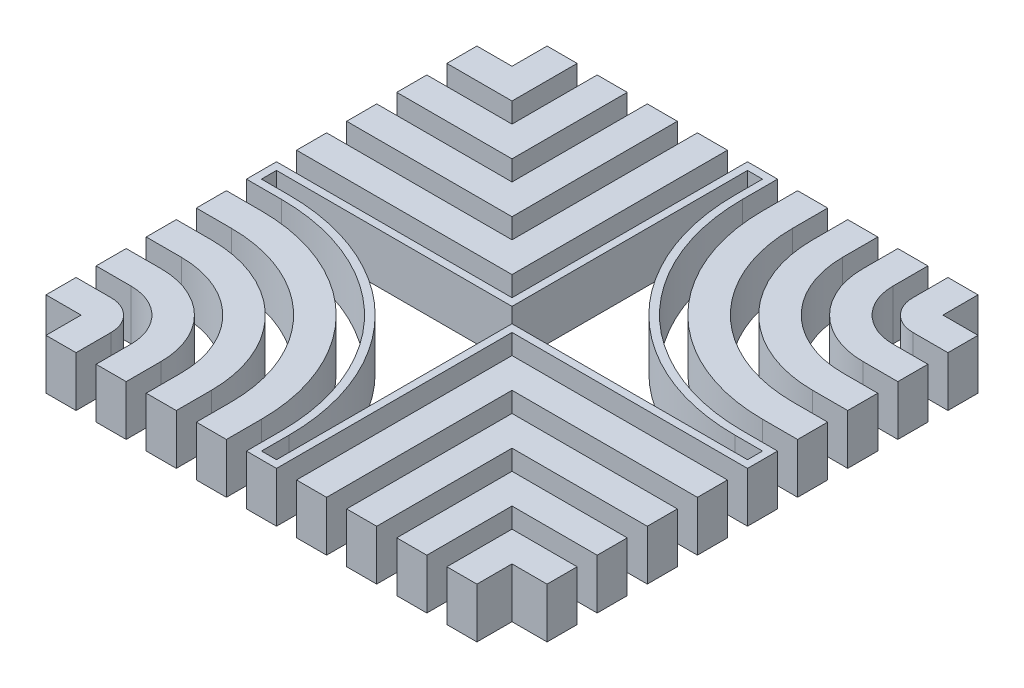
SolidWorks part; units mm, degrees
ref_plane "Front Plane" through (0, 0, 0) normal (0, 0, 1) x (1, 0, 0)
ref_plane "Top Plane" through (0, 0, 0) normal (0, 1, 0) x (1, 0, 0)
ref_plane "Right Plane" through (0, 0, 0) normal (1, 0, 0) x (0, 0, -1)
sketch "Sketch1" plane through (0, 0, 0) normal (0, 1, 0) x (1, 0, 0)
  line L0 (0, 50) -> (0, -50) construction
  line L1 (-50, 0) -> (50, 0) construction
  line L2 (-50, -10) -> (-10, -10) construction
  line L3 (-10, 50) -> (-10, 10) construction
  line L4 (-50, 10) -> (-10, 10) construction
  line L5 (10, 50) -> (10, 10) construction
  line L6 (10, 10) -> (50, 10) construction
  line L7 (-50, 10) -> (50, 10) construction
  line L8 (-10, -10) -> (-10, -50) construction
  line L9 (-10, 50) -> (-10, -50) construction
  line L10 (10, -10) -> (10, -50) construction
  line L11 (10, 50) -> (10, -50) construction
  line L12 (10, -10) -> (50, -10) construction
  line L13 (-50, -10) -> (50, -10) construction
  line L14 (-20, 50) -> (-20, 20) construction
  line L15 (-50, 20) -> (-20, 20) construction
  line L16 (20, 50) -> (20, 20) construction
  line L17 (20, 20) -> (50, 20) construction
  line L18 (20, -20) -> (20, -50) construction
  line L19 (20, -20) -> (50, -20) construction
  line L20 (-50, -20) -> (-20, -20) construction
  line L21 (-20, -20) -> (-20, -50) construction
  line L22 (-50, -30) -> (-30, -30) construction
  line L23 (-30, -30) -> (-30, -50) construction
  line L24 (30, -30) -> (30, -50) construction
  line L25 (30, -30) -> (50, -30) construction
  line L26 (30, 50) -> (30, 30) construction
  line L27 (30, 30) -> (50, 30) construction
  line L28 (-50, 30) -> (-30, 30) construction
  line L29 (-30, 50) -> (-30, 30) construction
  line L30 (-50, -40) -> (-40, -40) construction
  line L31 (-40, -40) -> (-40, -50) construction
  line L32 (40, -40) -> (40, -50) construction
  line L33 (40, -40) -> (50, -40) construction
  line L34 (-50, 40) -> (-40, 40) construction
  line L35 (-40, 50) -> (-40, 40) construction
  line L36 (40, 50) -> (40, 40) construction
  line L37 (40, 40) -> (50, 40) construction
  line L38 (-50, 37) -> (-37, 37)
  line L39 (-37, 50) -> (-37, 37)
  line L40 (-50, 27) -> (-27, 27)
  line L41 (-27, 50) -> (-27, 27)
  line L42 (-50, 17) -> (-17, 17)
  line L43 (-17, 50) -> (-17, 17)
  line L44 (-50, 7) -> (-7, 7)
  line L45 (-7, 50) -> (-7, 7)
  line L46 (-50, -3) -> (-43, -3)
  line L47 (-50, 43) -> (-43, 43)
  line L48 (-43, 50) -> (-43, 43)
  line L49 (-50, 33) -> (-33, 33)
  line L50 (-33, 50) -> (-33, 33)
  line L51 (-50, 23) -> (-23, 23)
  line L52 (-23, 50) -> (-23, 23)
  line L53 (-50, 13) -> (-13, 13)
  line L54 (-13, 50) -> (-13, 13)
  line L55 (-50, 3) -> (-3, 3)
  line L56 (-50, -13) -> (-43, -13)
  line L57 (-13, -43) -> (-13, -50)
  line L58 (-50, -23) -> (-43, -23)
  line L59 (-23, -43) -> (-23, -50)
  line L60 (-50, -33) -> (-43, -33)
  line L61 (-33, -43) -> (-33, -50)
  line L62 (-50, -43) -> (-43, -43)
  line L63 (-43, -43) -> (-43, -50)
  line L64 (7, -7) -> (50, -7)
  line L65 (7, -7) -> (7, -50)
  line L66 (17, -17) -> (50, -17)
  line L67 (17, -17) -> (17, -50)
  line L68 (27, -27) -> (50, -27)
  line L69 (27, -27) -> (27, -50)
  line L70 (37, -37) -> (50, -37)
  line L71 (37, -37) -> (37, -50)
  line L72 (7, 50) -> (7, 43)
  line L73 (43, 7) -> (50, 7)
  line L74 (-50, -7) -> (-43, -7)
  line L75 (-7, -43) -> (-7, -50)
  line L76 (-50, -17) -> (-43, -17)
  line L77 (-17, -43) -> (-17, -50)
  line L78 (-50, -27) -> (-43, -27)
  line L79 (-27, -43) -> (-27, -50)
  line L80 (-50, -37) -> (-43, -37)
  line L81 (-37, -43) -> (-37, -50)
  line L82 (13, -13) -> (50, -13)
  line L83 (13, -13) -> (13, -50)
  line L84 (23, -23) -> (50, -23)
  line L85 (23, -23) -> (23, -50)
  line L86 (33, -33) -> (50, -33)
  line L87 (33, -33) -> (33, -50)
  line L88 (43, -43) -> (50, -43)
  line L89 (43, -43) -> (43, -50)
  line L90 (13, 50) -> (13, 43)
  line L91 (43, 13) -> (50, 13)
  line L92 (17, 50) -> (17, 43)
  line L93 (43, 17) -> (50, 17)
  line L94 (23, 50) -> (23, 43)
  line L95 (43, 23) -> (50, 23)
  line L96 (27, 50) -> (27, 43)
  line L97 (43, 27) -> (50, 27)
  line L98 (37, 50) -> (37, 43)
  line L99 (43, 37) -> (50, 37)
  line L100 (33, 50) -> (33, 43)
  line L101 (43, 33) -> (50, 33)
  line L102 (43, 50) -> (43, 43)
  line L103 (43, 43) -> (50, 43)
  line L104 (-3, 50) -> (-3, 3)
  line L105 (3, 50) -> (3, 43)
  line L106 (-33, -50) -> (-27, -50)
  line L107 (-43, 50) -> (-37, 50)
  line L108 (-50, 43) -> (-50, 37)
  line L109 (-43, -50) -> (-37, -50)
  line L110 (50, 43) -> (50, 37)
  line L111 (-50, -7) -> (-7, -7) construction
  line L112 (-7, -7) -> (-7, -50) construction
  line L113 (-23, -50) -> (-17, -50)
  line L114 (-13, -50) -> (-7, -50)
  line L115 (-3, -50) -> (3, -50)
  line L116 (7, -50) -> (13, -50)
  line L117 (17, -50) -> (23, -50)
  line L118 (27, -50) -> (33, -50)
  line L119 (37, -50) -> (43, -50)
  line L120 (50, -37) -> (50, -43)
  line L121 (50, -27) -> (50, -33)
  line L122 (50, -17) -> (50, -23)
  line L123 (50, -7) -> (50, -13)
  line L124 (50, 3) -> (50, -3)
  line L125 (50, 13) -> (50, 7)
  line L126 (50, 23) -> (50, 17)
  line L127 (50, 33) -> (50, 27)
  line L128 (37, 50) -> (43, 50)
  line L129 (27, 50) -> (33, 50)
  line L130 (17, 50) -> (23, 50)
  line L131 (7, 50) -> (13, 50)
  line L132 (-3, 50) -> (3, 50)
  line L133 (-13, 50) -> (-7, 50)
  line L134 (-23, 50) -> (-17, 50)
  line L135 (-33, 50) -> (-27, 50)
  line L136 (-50, 33) -> (-50, 27)
  line L137 (-50, 23) -> (-50, 17)
  line L138 (-50, 13) -> (-50, 7)
  line L139 (-50, 3) -> (-50, -3)
  line L140 (-50, -7) -> (-50, -13)
  line L141 (-50, -17) -> (-50, -23)
  line L142 (-50, -27) -> (-50, -33)
  line L143 (-50, -37) -> (-50, -43)
  line L144 (43, 3) -> (50, 3)
  line L145 (-50, 3) -> (50, 3) construction
  line L146 (-3, -43) -> (-3, -50)
  line L147 (-3, 50) -> (-3, -50) construction
  line L148 (3, -3) -> (3, -50)
  line L149 (3, 50) -> (3, -50) construction
  line L150 (3, -3) -> (50, -3)
  line L151 (-50, -3) -> (50, -3) construction
  line L152 (-50, -13) -> (-13, -13) construction
  line L153 (-13, -13) -> (-13, -50) construction
  line L154 (-50, -17) -> (-17, -17) construction
  line L155 (-17, -17) -> (-17, -50) construction
  line L156 (-50, -23) -> (-23, -23) construction
  line L157 (-23, -23) -> (-23, -50) construction
  line L158 (-50, -27) -> (-27, -27) construction
  line L159 (-27, -27) -> (-27, -50) construction
  line L160 (-50, -33) -> (-33, -33) construction
  line L161 (-33, -33) -> (-33, -50) construction
  line L162 (-50, -37) -> (-37, -37) construction
  line L163 (-37, -37) -> (-37, -50) construction
  line L164 (37, 50) -> (37, 37) construction
  line L165 (37, 37) -> (50, 37) construction
  line L166 (33, 50) -> (33, 33) construction
  line L167 (33, 33) -> (50, 33) construction
  line L168 (27, 50) -> (27, 27) construction
  line L169 (27, 27) -> (50, 27) construction
  line L170 (23, 50) -> (23, 23) construction
  line L171 (23, 23) -> (50, 23) construction
  line L172 (17, 50) -> (17, 17) construction
  line L173 (17, 17) -> (50, 17) construction
  line L174 (13, 50) -> (13, 13) construction
  line L175 (13, 13) -> (50, 13) construction
  line L176 (7, 50) -> (7, 7) construction
  line L177 (7, 7) -> (50, 7) construction
  arc A0 (-43, -7) -> (-7, -43) centre (-43, -43) cw
  arc A1 (-43, -13) -> (-13, -43) centre (-43, -43) cw
  arc A2 (-43, -17) -> (-17, -43) centre (-43, -43) cw
  arc A3 (-43, -23) -> (-23, -43) centre (-43, -43) cw
  arc A4 (-43, -27) -> (-27, -43) centre (-43, -43) cw
  arc A5 (-43, -33) -> (-33, -43) centre (-43, -43) cw
  arc A6 (-43, -37) -> (-37, -43) centre (-43, -43) cw
  arc A7 (37, 43) -> (43, 37) centre (43, 43) ccw
  arc A8 (33, 43) -> (43, 33) centre (43, 43) ccw
  arc A9 (27, 43) -> (43, 27) centre (43, 43) ccw
  arc A10 (23, 43) -> (43, 23) centre (43, 43) ccw
  arc A11 (17, 43) -> (43, 17) centre (43, 43) ccw
  arc A12 (13, 43) -> (43, 13) centre (43, 43) ccw
  arc A13 (7, 43) -> (43, 7) centre (43, 43) ccw
  arc A14 (43, 3) -> (3, 43) centre (43, 43) cw
  arc A15 (-3, -43) -> (-43, -3) centre (-43, -43) ccw
  point P4 (0, 0)
  point P8 (0, 0)
  dimension "D21" = 6
  dimension "D22" = 10
  dimension "D23" = 16
  dimension "D24" = 20
  dimension "D25" = 26
  dimension "D26" = 30
  dimension "D27" = 36
  dimension "D28" = 6
  dimension "D29" = 10
  dimension "D30" = 16
  dimension "D31" = 20
  dimension "D32" = 26
  dimension "D33" = 30
  dimension "D34" = 36
  dimension "D35" = 40
  dimension "D36" = 40
  dimension "D1" = 100
  dimension "D2" = 100
  dimension "D3" = 10
  dimension "D4" = 10
  dimension "D5" = 10
  dimension "D6" = 10
  dimension "D7" = 10
  dimension "D8" = 10
  dimension "D9" = 10
  dimension "D10" = 10
  dimension "D11" = 3
  dimension "D12" = 3
  dimension "D13" = 3
  dimension "D14" = 3
  dimension "D15" = 3
  dimension "D16" = 3
  dimension "D17" = 3
  dimension "D18" = 3
  dimension "D19" = 3
  dimension "D20" = 3
extrude "Boss-Extrude1" add sketch "Sketch1" along normal blind 10
shell "Shell1" thickness 1.5
